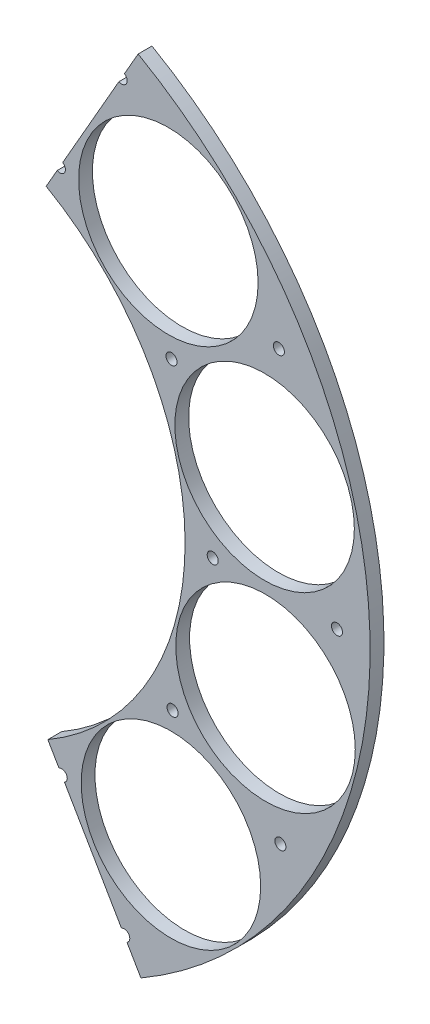
SolidWorks part; units mm, degrees
ref_plane "Plan de face" through (0, 0, 0) normal (0, 0, 1) x (1, 0, 0)
ref_plane "Plan de dessus" through (0, 0, 0) normal (0, 1, 0) x (1, 0, 0)
ref_plane "Plan de droite" through (0, 0, 0) normal (1, 0, 0) x (0, 0, -1)
sketch "Esquisse1" plane through (0, 0, 0) normal (0, 0, 1) x (1, 0, 0)
  line L2 (-2, 166.988) -> (-2, 99.98)
  line L3 (-2, -99.98) -> (-2, -166.988)
  arc A1 (0, -133.5) -> (0, 133.5) centre (0, 0) ccw
  circle A3 centre (33.9222, 129.1183) radius 32.5
  circle A7 centre (93.9366, 94.8586) radius 32.5
  circle A8 centre (128.7808, 35.1817) radius 32.5
  circle A9 centre (129.1183, -33.9222) radius 32.5
  circle A10 centre (94.8586, -93.9366) radius 32.5
  circle A11 centre (35.1817, -128.7808) radius 32.5
  arc A12 (-2, -166.988) -> (-2, 166.988) centre (0, 0) ccw
  arc A13 (-2, -99.98) -> (-2, 99.98) centre (0, 0) ccw
  circle A18 centre (-35.1817, 128.7808) radius 32.5 [skipped]
  circle A19 centre (-94.8586, 93.9366) radius 32.5 [skipped]
  circle A20 centre (-129.1183, 33.9222) radius 32.5 [skipped]
  circle A21 centre (-128.7808, -35.1817) radius 32.5 [skipped]
  circle A22 centre (-93.9366, -94.8586) radius 32.5 [skipped]
  circle A23 centre (-33.9222, -129.1183) radius 32.5 [skipped]
  point P0 (0, 0)
  point P1 (133.5, 0)
  point P4 (102, 0)
  point P5 (0, 0)
  point P7 (0, 165)
  point P8 (0, 102)
  point P9 (0, -102)
  point P10 (0, -165)
  point P11 (157.7903, 48.2413)
  point P42 (0, 0)
  dimension "D1" = 65
  dimension "D4" = 12
extrude "Boss.-Extru.2" add sketch "Esquisse1" along normal blind 5
sketch "Esquisse2" plane through (0, 0, 0) normal (0, 0, -1) x (-1, 0, 0)
  line L0 (-77.0319, 134.5031) -> (0, 0) construction
  circle A0 centre (-77.0319, 134.5031) radius 2
  circle A1 centre (-54.6678, 95.4538) radius 2
  circle A16 centre (-77.9671, -133.9632) radius 2
  circle A17 centre (-55.3315, -95.0706) radius 2
  circle A18 centre (-134.5031, -77.0319) radius 2
  circle A19 centre (-95.4538, -54.6678) radius 2
  circle A20 centre (-154.9991, 0.5399) radius 2
  circle A21 centre (-109.9993, 0.3832) radius 2
  circle A22 centre (-133.9632, 77.9671) radius 2
  circle A23 centre (-95.0706, 55.3315) radius 2
  circle A24 centre (77.9671, 133.9632) radius 2 [skipped]
  circle A25 centre (0.5399, 154.9991) radius 2 [skipped]
  circle A26 centre (0.3832, 109.9993) radius 2 [skipped]
  circle A27 centre (-0.3832, -109.9993) radius 2 [skipped]
  circle A28 centre (-0.5399, -154.9991) radius 2 [skipped]
  circle A29 centre (55.3315, 95.0706) radius 2 [skipped]
  circle A30 centre (134.5031, 77.0319) radius 2 [skipped]
  circle A31 centre (95.4538, 54.6678) radius 2 [skipped]
  circle A32 centre (154.9991, -0.5399) radius 2 [skipped]
  circle A33 centre (109.9993, -0.3832) radius 2 [skipped]
  circle A34 centre (133.9632, -77.9671) radius 2 [skipped]
  circle A35 centre (95.0706, -55.3315) radius 2 [skipped]
  circle A36 centre (77.0319, -134.5031) radius 2 [skipped]
  circle A37 centre (54.6678, -95.4538) radius 2 [skipped]
  point P53 (0, 0)
  dimension "D4" = 4
  dimension "D5" = 4
  dimension "D1" = 155
  dimension "D2" = 45
  dimension "D3" = 12
extrude "Enlèv. mat.-Extru.1" cut sketch "Esquisse2" against normal blind 5
sketch "Esquisse3" plane through (0, 0, 5) normal (0, 0, 1) x (1, 0, 0)
  line L0 (0, 0) -> (77.0319, 134.5031)
  line L1 (77.0319, 134.5031) -> (82.9957, 144.9162)
  line L2 (82.9957, 144.9162) -> (91.6245, 157.4747)
  line L3 (91.6245, 157.4747) -> (25.3138, 172.4848)
  line L4 (25.3138, 172.4848) -> (-36.1515, 181.6135)
  line L5 (-36.1515, 181.6135) -> (-51.5697, -183.2371)
  line L6 (-51.5697, -183.2371) -> (77.0319, -179.1466)
  line L7 (77.0319, -179.1466) -> (82.9957, -170.8305)
  line L8 (0, 0) -> (77.9671, -133.9632)
  line L9 (77.9671, -133.9632) -> (84.0033, -144.3345)
  line L10 (84.0033, -144.3345) -> (82.9957, -170.8305)
  arc A0 (-2, -166.988) -> (-2, 166.988) centre (0, 0) ccw construction
extrude "Enlèv. mat.-Extru.2" cut sketch "Esquisse3" against normal blind 10
